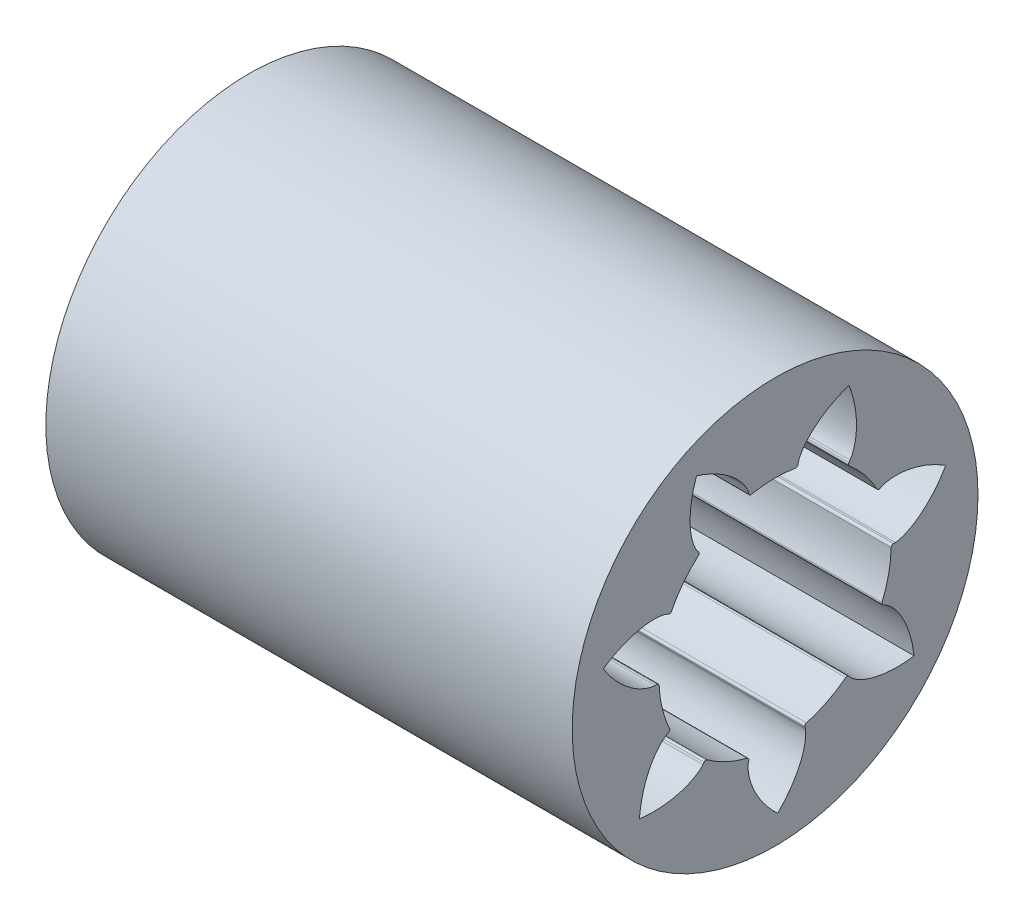
SolidWorks part; units mm, degrees
material "AISI 1020 Steel, Cold Rolled"
ref_plane "Front Plane" through (0, 0, 0) normal (0, 0, 1) x (1, 0, 0)
ref_plane "Top Plane" through (0, 0, 0) normal (0, 1, 0) x (1, 0, 0)
ref_plane "Right Plane" through (0, 0, 0) normal (1, 0, 0) x (0, 0, -1)
sketch "Sketch1" plane through (0, 0, 0) normal (1, 0, 0) x (0, 0, -1)
  circle A0 centre (0, 0) radius 11.0998
  circle A1 centre (0, 0) radius 6.35
  dimension "D1" = 22.1996
  dimension "D2" = 12.7
extrude "Boss-Extrude1" add sketch "Sketch1" along normal blind 28.7909
sketch "Sketch2" plane through (28.7909, 0, 0) normal (1, 0, 0) x (0, 0, -1)
  line L0 (6.4741, -0.0012) -> (6.5782, -0.0012)
  line L1 (6.0092, -2.6773) -> (5.9141, -2.6349)
  line L2 (4.0367, -5.0626) -> (4.1016, -5.1439)
  line L3 (1.6545, -6.3676) -> (1.6284, -6.2669)
  line L4 (-1.4402, -6.3126) -> (-1.4634, -6.4141)
  line L5 (-3.9458, -5.2639) -> (-3.8834, -5.1806)
  line L6 (-5.8323, -2.81) -> (-5.9261, -2.8552)
  line L7 (-6.5746, -0.1972) -> (-6.4706, -0.1941)
  line L8 (-5.8323, 2.8077) -> (-5.9261, 2.8529)
  line L9 (-4.2523, 5.0171) -> (-4.1851, 4.9377)
  line L10 (-1.4402, 6.3103) -> (-1.4634, 6.4118)
  line L11 (1.2723, 6.4525) -> (1.2521, 6.3505)
  line L12 (4.0367, 5.0603) -> (4.1016, 5.1416)
  line L13 (5.8391, 3.0282) -> (5.7467, 2.9803)
  arc A0 (6.4741, -0.0012) -> (6.3492, -0.1237) centre (6.4741, -0.1262) ccw
  arc A1 (5.8499, -2.4721) -> (6.3492, -0.1237) centre (0.0003, -0.0012) ccw
  arc A2 (5.8499, -2.4721) -> (5.9141, -2.6349) centre (5.965, -2.5208) ccw
  arc A3 (4.0367, -5.0626) -> (3.8629, -5.0413) centre (3.939, -5.1405) ccw
  arc A4 (1.7156, -6.1151) -> (3.8629, -5.0413) centre (0.0003, -0.0012) ccw
  arc A5 (1.7156, -6.1151) -> (1.6284, -6.2669) centre (1.7493, -6.2355) ccw
  arc A6 (-1.4402, -6.3126) -> (-1.5319, -6.1635) centre (-1.5621, -6.2848) ccw
  arc A7 (-3.7103, -5.1542) -> (-1.5319, -6.1635) centre (0.0003, -0.0012) ccw
  arc A8 (-3.7103, -5.1542) -> (-3.8834, -5.1806) centre (-3.7834, -5.2556) ccw
  arc A9 (-5.8323, -2.81) -> (-5.7729, -2.6454) centre (-5.8866, -2.6974) ccw
  arc A10 (-6.342, -0.3129) -> (-5.7729, -2.6454) centre (0.0003, -0.0012) ccw
  arc A11 (-6.342, -0.3129) -> (-6.4706, -0.1941) centre (-6.4669, -0.319) ccw
  arc A12 (-5.8323, 2.8077) -> (-5.6666, 2.8639) centre (-5.7781, 2.9203) ccw
  arc A13 (-4.1978, 4.7631) -> (-5.6666, 2.8639) centre (0.0003, -0.0012) ccw
  arc A14 (-4.1978, 4.7631) -> (-4.1851, 4.9377) centre (-4.2804, 4.8569) ccw
  arc A15 (-1.4402, 6.3103) -> (-1.2929, 6.2158) centre (-1.3184, 6.3381) ccw
  arc A16 (1.1077, 6.2515) -> (-1.2929, 6.2158) centre (0.0003, -0.0012) ccw
  arc A17 (1.1077, 6.2515) -> (1.2521, 6.3505) centre (1.1295, 6.3746) ccw
  arc A18 (4.0367, 5.0603) -> (4.0546, 4.8861) centre (4.1344, 4.9823) ccw
  arc A19 (5.5793, 3.0316) -> (4.0546, 4.8861) centre (0.0003, -0.0012) ccw
  arc A20 (5.5793, 3.0316) -> (5.7467, 2.9803) centre (5.6891, 3.0913) ccw
  spline S0 degree 3 poles (6.0092, -2.6773) (6.0443, -2.6929) (6.0769, -2.7138) (6.1408, -2.7565) (6.1718, -2.7793) (6.2625, -2.8506) (6.3199, -2.902) (6.4846, -3.0636) (6.5845, -3.1812) (6.86, -3.5514) (7.0114, -3.8213) (7.388, -4.6639) (7.5355, -5.269) (7.603, -5.8806) knots 0 0 0 0 0.03125 0.03125 0.0625 0.0625 0.125 0.125 0.25 0.25 0.5 0.5 1 1 1 1
  spline S1 degree 3 poles (7.603, -5.8806) (6.9941, -5.9691) (6.3713, -5.9787) (5.461, -5.8261) (5.1616, -5.7475) (4.734, -5.574) (4.5951, -5.5069) (4.3972, -5.3881) (4.3331, -5.3455) (4.2412, -5.2757) (4.2114, -5.2514) (4.1539, -5.2002) (4.1255, -5.174) (4.1016, -5.1439) knots 0 0 0 0 0.5 0.5 0.75 0.75 0.875 0.875 0.9375 0.9375 0.96875 0.96875 1 1 1 1
  spline S2 degree 3 poles (1.6545, -6.3676) (1.6642, -6.4048) (1.6682, -6.4433) (1.6747, -6.5199) (1.6762, -6.5584) (1.677, -6.6737) (1.6726, -6.7506) (1.6489, -6.9802) (1.6192, -7.1316) (1.5016, -7.5778) (1.385, -7.8645) (0.961, -8.6843) (0.5798, -9.1768) (0.1438, -9.6109) knots 0 0 0 0 0.03125 0.03125 0.0625 0.0625 0.125 0.125 0.25 0.25 0.5 0.5 1 1 1 1
  spline S3 degree 3 poles (0.1438, -9.6109) (-0.305, -9.1901) (-0.7008, -8.7091) (-1.1491, -7.9023) (-1.2743, -7.6192) (-1.4052, -7.1767) (-1.4394, -7.0262) (-1.4699, -6.7975) (-1.4767, -6.7208) (-1.4793, -6.6054) (-1.4789, -6.567) (-1.4747, -6.4902) (-1.4719, -6.4516) (-1.4634, -6.4141) knots 0 0 0 0 0.5 0.5 0.75 0.75 0.875 0.875 0.9375 0.9375 0.96875 0.96875 1 1 1 1
  spline S4 degree 3 poles (-7.4234, -6.1049) (-7.3742, -5.4916) (-7.245, -4.8823) (-6.8937, -4.0288) (-6.7504, -3.7544) (-6.4861, -3.3761) (-6.3898, -3.2556) (-6.23, -3.0891) (-6.1742, -3.036) (-6.0856, -2.962) (-6.0553, -2.9383) (-5.9927, -2.8937) (-5.9608, -2.8719) (-5.9261, -2.8552) knots 0 0 0 0 0.5 0.5 0.75 0.75 0.875 0.875 0.9375 0.9375 0.96875 0.96875 1 1 1 1
  spline S5 degree 3 poles (-6.5746, -0.1972) (-6.613, -0.1984) (-6.6514, -0.1937) (-6.7276, -0.1829) (-6.7654, -0.1758) (-6.878, -0.151) (-6.952, -0.1296) (-7.1705, -0.0554) (-7.3115, 0.0072) (-7.7204, 0.2212) (-7.974, 0.3987) (-8.6788, 0.9944) (-9.0742, 1.4757) (-9.4004, 1.9973) knots 0 0 0 0 0.03125 0.03125 0.0625 0.0625 0.125 0.125 0.25 0.25 0.5 0.5 1 1 1 1
  spline S6 degree 3 poles (-9.4004, 1.9973) (-8.8902, 2.3412) (-8.3332, 2.6201) (-7.4469, 2.8777) (-7.1431, 2.9367) (-6.6825, 2.9659) (-6.5282, 2.9657) (-6.2985, 2.9446) (-6.2221, 2.9341) (-6.1091, 2.911) (-6.0717, 2.9021) (-5.9977, 2.8809) (-5.9608, 2.8696) (-5.9261, 2.8529) knots 0 0 0 0 0.5 0.5 0.75 0.75 0.875 0.875 0.9375 0.9375 0.96875 0.96875 1 1 1 1
  spline S7 degree 3 poles (-4.2523, 5.0171) (-4.2772, 5.0464) (-4.2975, 5.0794) (-4.3366, 5.1456) (-4.3546, 5.1796) (-4.4054, 5.2832) (-4.4348, 5.3544) (-4.5131, 5.5714) (-4.552, 5.7207) (-4.6396, 6.1738) (-4.659, 6.4827) (-4.6327, 7.4052) (-4.5029, 8.0144) (-4.2985, 8.5947) knots 0 0 0 0 0.03125 0.03125 0.0625 0.0625 0.125 0.125 0.25 0.25 0.5 0.5 1 1 1 1
  spline S8 degree 3 poles (-4.2985, 8.5947) (-3.7115, 8.4102) (-3.1462, 8.1486) (-2.3922, 7.6163) (-2.1566, 7.4155) (-1.8466, 7.0736) (-1.7505, 6.9529) (-1.6238, 6.7601) (-1.5845, 6.6938) (-1.5321, 6.5911) (-1.5157, 6.5563) (-1.4861, 6.4852) (-1.4719, 6.4493) (-1.4634, 6.4118) knots 0 0 0 0 0.5 0.5 0.75 0.75 0.875 0.875 0.9375 0.9375 0.96875 0.96875 1 1 1 1
  spline S9 degree 3 poles (1.2723, 6.4525) (1.2797, 6.4903) (1.2928, 6.5267) (1.3202, 6.5985) (1.3355, 6.6338) (1.3849, 6.7381) (1.4222, 6.8055) (1.5431, 7.002) (1.6355, 7.1255) (1.9351, 7.4765) (2.1646, 7.6842) (2.9022, 8.2389) (3.4594, 8.5173) (4.0406, 8.7192) knots 0 0 0 0 0.03125 0.03125 0.0625 0.0625 0.125 0.125 0.25 0.25 0.5 0.5 1 1 1 1
  spline S10 degree 3 poles (4.0406, 8.7192) (4.2624, 8.1453) (4.4103, 7.5402) (4.4642, 6.6188) (4.4541, 6.3094) (4.3801, 5.8539) (4.3456, 5.7035) (4.2738, 5.4842) (4.2466, 5.4122) (4.1989, 5.3071) (4.1819, 5.2726) (4.1448, 5.2052) (4.1255, 5.1717) (4.1016, 5.1416) knots 0 0 0 0 0.5 0.5 0.75 0.75 0.875 0.875 0.9375 0.9375 0.96875 0.96875 1 1 1 1
  spline S11 degree 3 poles (5.8391, 3.0282) (5.8732, 3.0459) (5.9098, 3.0584) (5.9831, 3.0818) (6.0203, 3.0918) (6.1325, 3.1182) (6.2085, 3.1311) (6.4375, 3.1591) (6.5917, 3.1638) (7.0529, 3.1484) (7.3584, 3.0985) (8.252, 2.8676) (8.817, 2.6056) (9.3373, 2.2771) knots 0 0 0 0 0.03125 0.03125 0.0625 0.0625 0.125 0.125 0.25 0.25 0.5 0.5 1 1 1 1
  spline S12 degree 3 poles (9.3373, 2.2771) (9.0268, 1.7459) (8.646, 1.253) (7.9592, 0.6364) (7.711, 0.4514) (7.3087, 0.2252) (7.1697, 0.1584) (6.9535, 0.0778) (6.8801, 0.0541) (6.7683, 0.0259) (6.7307, 0.0177) (6.6549, 0.0047) (6.6166, -0.0012) (6.5782, -0.0012) knots 0 0 0 0 0.5 0.5 0.75 0.75 0.875 0.875 0.9375 0.9375 0.96875 0.96875 1 1 1 1
  spline S13 degree 3 poles (-3.9458, -5.2639) (-3.9689, -5.2946) (-3.9965, -5.3217) (-4.0523, -5.3746) (-4.0815, -5.3997) (-4.1711, -5.4723) (-4.234, -5.5168) (-4.4282, -5.6414) (-4.5651, -5.7126) (-4.9873, -5.8988) (-5.2842, -5.9864) (-6.1894, -6.1661) (-6.8122, -6.1752) (-7.4234, -6.1049) knots 0 0 0 0 0.03125 0.03125 0.0625 0.0625 0.125 0.125 0.25 0.25 0.5 0.5 1 1 1 1
extrude "Cut-Extrude1" cut sketch "Sketch2" against normal through all
